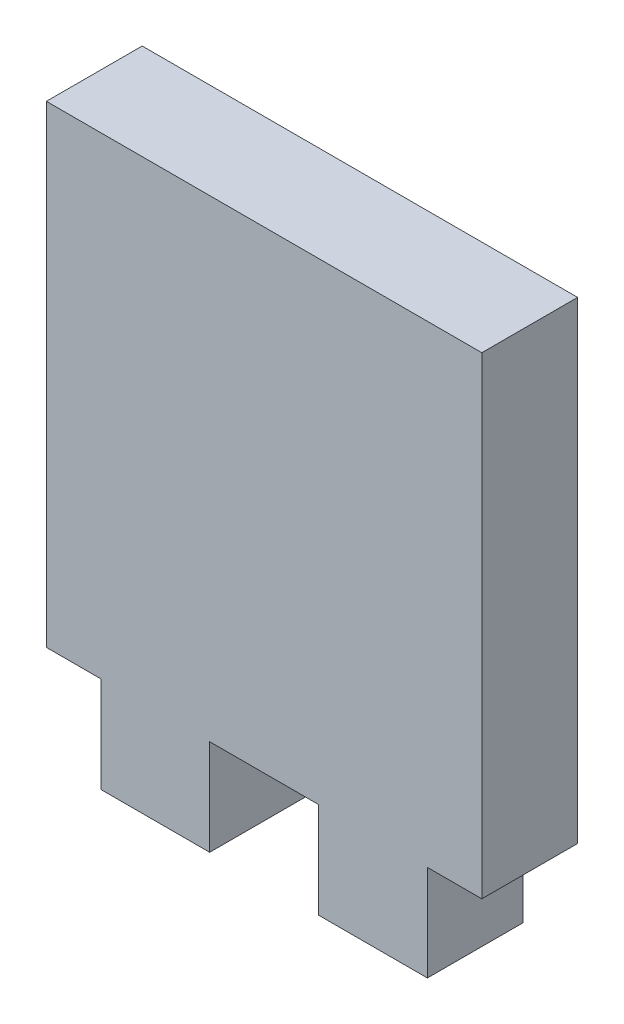
SolidWorks part; units mm, degrees
ref_plane "Front Plane" through (0, 0, 0) normal (0, 0, 1) x (1, 0, 0)
ref_plane "Top Plane" through (0, 0, 0) normal (0, 1, 0) x (1, 0, 0)
ref_plane "Right Plane" through (0, 0, 0) normal (1, 0, 0) x (0, 0, -1)
sketch "Sketch1" plane through (0, 0, 0) normal (0, 0, 1) x (1, 0, 0)
  line L0 (15.875, -2.794) -> (9.525, -2.794) construction
  line L1 (0, 0) -> (3.175, 0)
  line L2 (0, 0) -> (0, 27.588)
  line L3 (0, 27.588) -> (25.4, 27.588)
  line L4 (25.4, 0) -> (25.4, 27.588)
  line L6 (3.175, 0) -> (3.175, -5.588)
  line L7 (3.175, -5.588) -> (9.525, -5.588)
  line L8 (9.525, 0) -> (9.525, -5.588)
  line L10 (15.875, 0) -> (15.875, -5.588)
  line L11 (15.875, -5.588) -> (22.225, -5.588)
  line L12 (22.225, 0) -> (22.225, -5.588)
  line L13 (9.525, -2.794) -> (12.7, -2.794) construction
  line L14 (12.7, -2.794) -> (12.7, 27.588) construction
  line L15 (9.525, 0) -> (15.875, 0)
  line L16 (22.225, 0) -> (25.4, 0)
  point P15 (12.7, 0)
  point P18 (29.2151, 0)
  dimension "D1" = 5.588
  dimension "D2" = 6.35
  dimension "D3" = 6.35
  dimension "D4" = 25.4
  dimension "D5" = 27.588
  dimension "D6" = 12.7
  dimension "D7" = 2.794
extrude "Boss-Extrude1" add sketch "Sketch1" along normal blind 5.588
